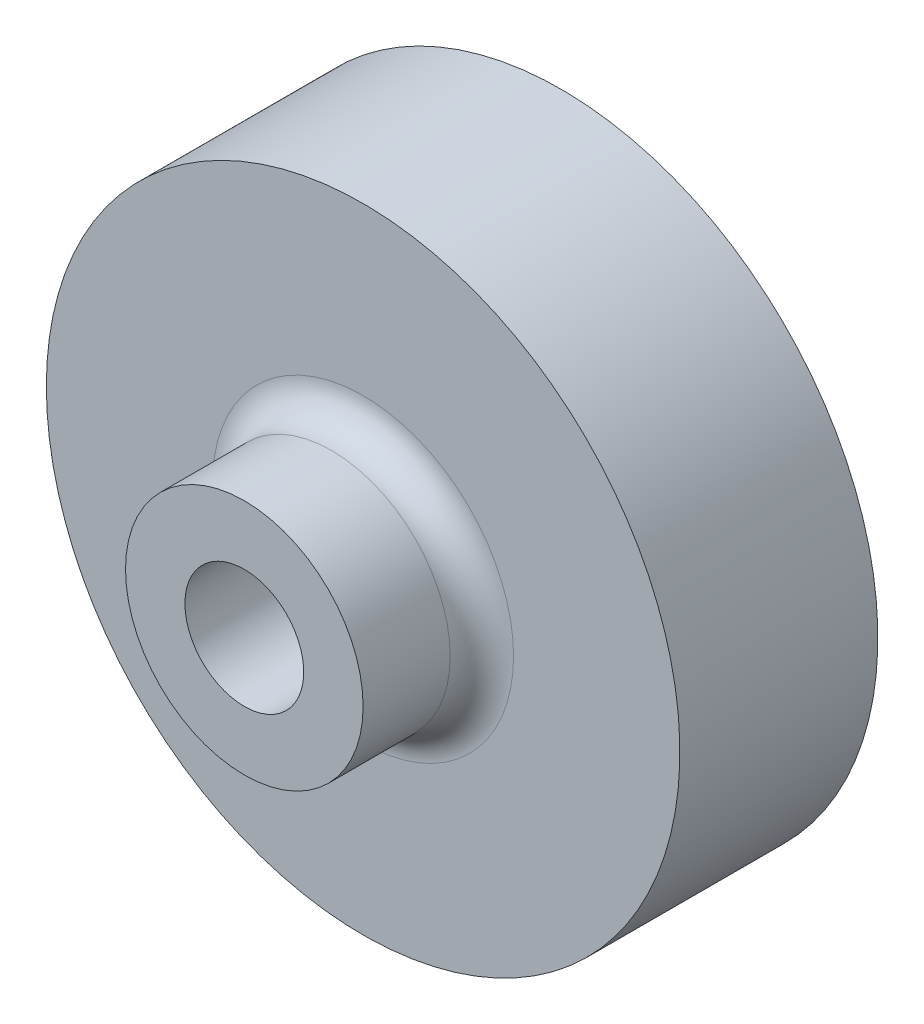
SolidWorks part; units mm, degrees
material "Plain Carbon Steel"
ref_plane "Front Plane" through (0, 0, 0) normal (0, 0, 1) x (1, 0, 0)
ref_plane "Top Plane" through (0, 0, 0) normal (0, 1, 0) x (1, 0, 0)
ref_plane "Right Plane" through (0, 0, 0) normal (1, 0, 0) x (0, 0, -1)
sketch "Sketch1" plane through (0, 0, 0) normal (0, 1, 0) x (1, 0, 0)
  line L0 (0, 87.4068) -> (0, -86.6671) construction
  line L1 (0, -55) -> (0, 55) construction
  line L2 (0, 0) -> (-9.525, 0)
  line L3 (-55, 0) -> (55, 0) construction
  line L4 (-9.525, 0) -> (-9.525, 9.525)
  line L5 (-9.525, 9.525) -> (-25.4, 9.525)
  line L6 (-25.4, 9.525) -> (-25.4, 25.4)
  line L7 (-25.4, 25.4) -> (0, 25.4)
  line L8 (0, 25.4) -> (0, 0)
  dimension "D1" = 25.4
  dimension "D2" = 15.875
  dimension "D3" = 9.525
  dimension "D4" = 9.525
revolve "Revolve1" add sketch "Sketch1" angle 360 about L0
sketch "Sketch2" plane through (0, 0, -25.4) normal (0, 0, -1) x (-1, 0, 0)
  line L0 (-1.27, 4.59) -> (-1.27, -4.59)
  line L1 (1.27, 4.59) -> (1.27, -4.59)
  line L2 (0, 44.1881) -> (0, -37.2622) construction
  line L3 (0, 55) -> (0, -55) construction
  circle A0 centre (0, 0) radius 4.7625
  arc A1 (-1.27, 4.59) -> (1.27, 4.59) centre (0, 0) cw
  arc A2 (-1.27, -4.59) -> (1.27, -4.59) centre (0, 0) ccw
  dimension "D1" = 9.525
  dimension "D2" = 2.54
extrude "Cut-Extrude1" cut sketch "Sketch2" against normal through all contours L0 A0 | L1 A0
sketch "Sketch3" plane through (0, 0, 0) normal (0, 0, 1) x (1, 0, 0)
  line L0 (-1.27, 4.59) -> (-1.27, -4.59)
  line L2 (1.27, -4.59) -> (1.27, 4.59)
  circle A0 centre (0, 0) radius 4.7625
  arc A1 (-1.27, 4.59) -> (1.27, 4.59) centre (0, 0) cw
  arc A2 (-1.27, -4.59) -> (1.27, -4.59) centre (0, 0) ccw
  line M1 (-1.27, 4.59) -> (-1.27, -4.59)
  line M5 (1.27, -4.59) -> (1.27, 4.59)
  dimension "D1" = 9.525
extrude "Cut-Extrude2" cut sketch "Sketch3" against normal blind 22.225 contours A0 M5 M1
fillet "Fillet1" radius 2.54 1 edges at (-9.525, 0, -9.525)
